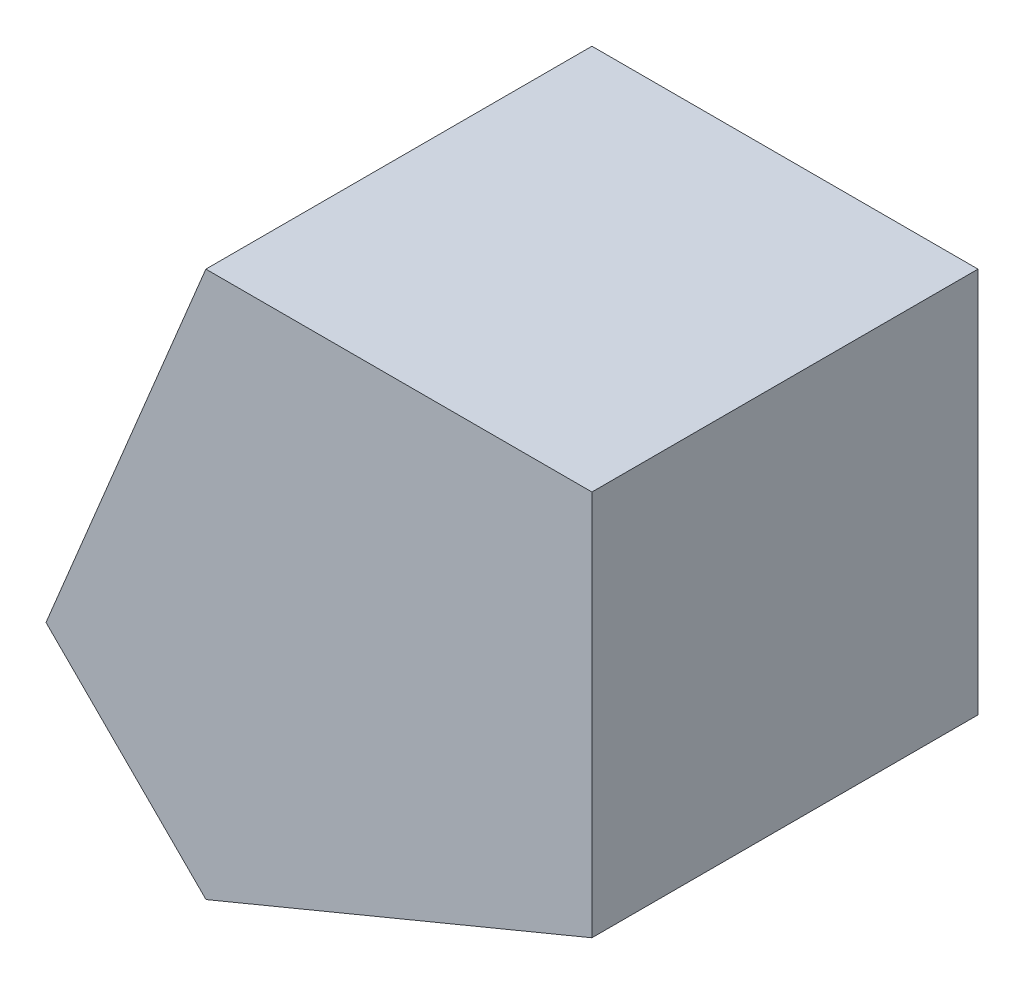
SolidWorks part; units mm, degrees
ref_plane "前视基准面" through (0, 0, 0) normal (0, 0, 1) x (1, 0, 0)
ref_plane "上视基准面" through (0, 0, 0) normal (0, 1, 0) x (1, 0, 0)
ref_plane "右视基准面" through (0, 0, 0) normal (1, 0, 0) x (0, 0, -1)
sketch "草图1" plane through (0, 0, 0) normal (0, 0, 1) x (1, 0, 0)
  line L0 (16.6248, 6.2471) -> (16.6248, 16.2471)
  line L1 (16.6248, 16.2471) -> (6.6248, 16.2471)
  line L2 (6.6248, 16.2471) -> (2.4841, 6.2507)
  line L3 (6.6284, 2.1065) -> (16.6248, 6.2471)
  line L4 (6.6284, 2.1065) -> (2.4841, 6.2507)
  dimension "D1" = 10
  dimension "D2" = 10.82
  dimension "D3" = 112.5
  dimension "D4" = 112.5
extrude "凸台-拉伸1" add sketch "草图1" along normal blind 10
